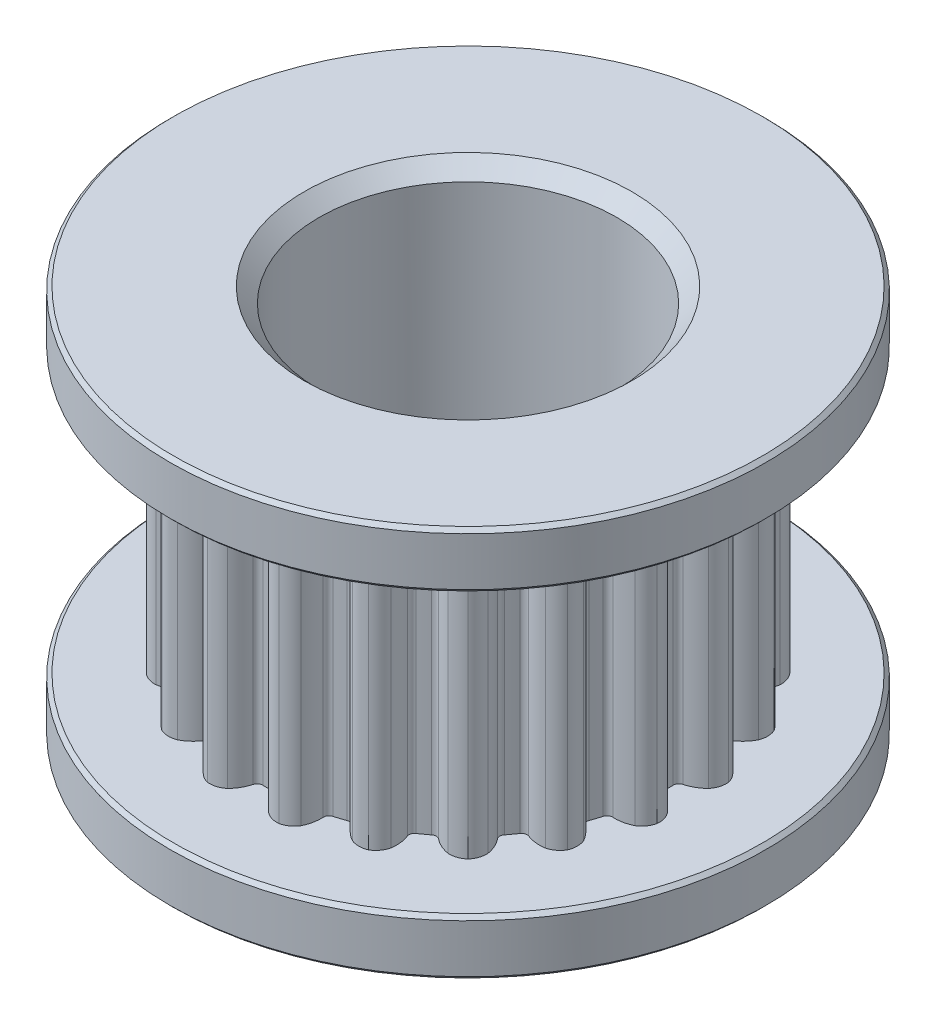
SolidWorks part; units mm, degrees
material "6061 Alloy"
ref_plane "Front Plane" through (0, 0, 0) normal (0, 0, 1) x (1, 0, 0)
ref_plane "Top Plane" through (0, 0, 0) normal (0, 1, 0) x (1, 0, 0)
ref_plane "Right Plane" through (0, 0, 0) normal (1, 0, 0) x (0, 0, -1)
sketch "BodyS" plane through (0, 0, 0) normal (0, 0, 1) x (1, 0, 0)
  line L0 (6.11, -3.75) -> (6.11, 3.75)
  line L1 (6.11, 3.75) -> (8, 3.75)
  line L2 (8, 3.75) -> (8, 5.25)
  line L3 (8, 5.25) -> (4, 5.25)
  line L4 (4, 5.25) -> (4, 2.25)
  line L5 (4, 2.25) -> (3.5, 2.25)
  line L6 (3.5, 2.25) -> (3.5, -2.25)
  line L7 (3.5, -2.25) -> (4, -2.25)
  line L8 (4, -2.25) -> (4, -5.25)
  line L9 (4, -5.25) -> (8, -5.25)
  line L10 (8, -5.25) -> (8, -3.75)
  line L11 (8, -3.75) -> (6.11, -3.75)
  line L12 (0, 0) -> (3.5, 0) construction
  line L13 (0, 5.25) -> (0, -5.25) construction
  dimension "BearingOD" = 8
  dimension "Height" = 10.5
  dimension "FlangeHeight" = 1.5
  dimension "BearingHeight" = 3
  dimension "BearingRestDiaControl" = 0.5
  dimension "RefBodyInnerDiameter" = 7
  dimension "FlangeDiaControl" = 4
  dimension "RefFlangeDia" = 16
  dimension "BeltPathDiaControl" = 2.11
  dimension "RefBeltPathDia" = 12.22
revolve "Body" add sketch "BodyS" angle 360 about L13
sketch "GT2ProfileS" plane through (0, 0, 0) normal (0, 1, 0) x (1, 0, 0)
  line L1 (0, -6.11) -> (0, -5.36) construction
  line L2 (-0.9955, -6.0283) -> (-0.8733, -5.2884) construction
  line L3 (0, 0) -> (-0.8733, -5.2884) construction
  line L4 (0.9955, -6.0283) -> (0, 0) construction
  arc A3 (0.2997, -5.4688) -> (0.1507, -5.3579) centre (0.1549, -5.5078) ccw
  arc A4 (-0.9955, -6.0283) -> (0.9955, -6.0283) centre (0, 0) ccw
  arc A5 (-0.2997, -5.4688) -> (-0.1507, -5.3579) centre (-0.1549, -5.5078) cw
  arc A6 (-0.2997, -5.4688) -> (-0.5497, -5.907) centre (-1.2653, -5.2085) cw
  circle A7 centre (0, 0) radius 6.11 construction
  arc A8 (-0.1507, -5.3579) -> (0.1507, -5.3579) centre (0, 0) ccw
  arc A9 (-0.5497, -5.907) -> (-0.9955, -6.0283) centre (-0.9051, -5.4808) cw
  arc A10 (0.2997, -5.4688) -> (0.5497, -5.907) centre (1.2653, -5.2085) ccw
  arc A11 (0.5497, -5.907) -> (0.9955, -6.0283) centre (0.9051, -5.4808) ccw
  circle A12 centre (0, 0) radius 5.36 construction
  dimension "BottomRadius" = 0.15
  dimension "MidRadius" = 1
  dimension "TopRadius" = 0.555
  dimension "Height" = 0.75
  dimension "XDistMidRadius" = 0.4
  dimension "ArcLengthAngle" = 18.755
  dimension "ArcLength" = 2
sketch "ThruBoreS" plane through (0, 0, 0) normal (0, 1, 0) x (1, 0, 0)
  circle A0 centre (0, 0) radius 4
  circle A2 centre (0, 0) radius 4 construction
extrude "ThruBore" cut sketch "ThruBoreS" against normal through all both and the other way through all
extrude "GT2Profile" cut sketch "GT2ProfileS" against normal up to surface (3.75 mm away) and the other way up to surface (3.75 mm away) up to face at (0, -3.75, 6.11) other way up to face at (0, 3.75, 8)
pattern_circular "GT2 Groove CP" count 20 over 360 about axis through (0, 0, 0) along (0, 1, 0) of "GT2Profile"
chamfer "InnerC" distance 0.4 angle 45 2 edges at (0, -5.25, 4) (0, 5.25, 4)
chamfer "OuterC" distance 0.1 angle 45 4 edges at (0, -5.25, 8) (0, -3.75, 8) (0, 3.75, 8) (0, 5.25, 8)
equation "\"NumTeeth@GT2 Groove CP\"=int(360/\"ArcLengthAngle@GT2ProfileS\")+1"
